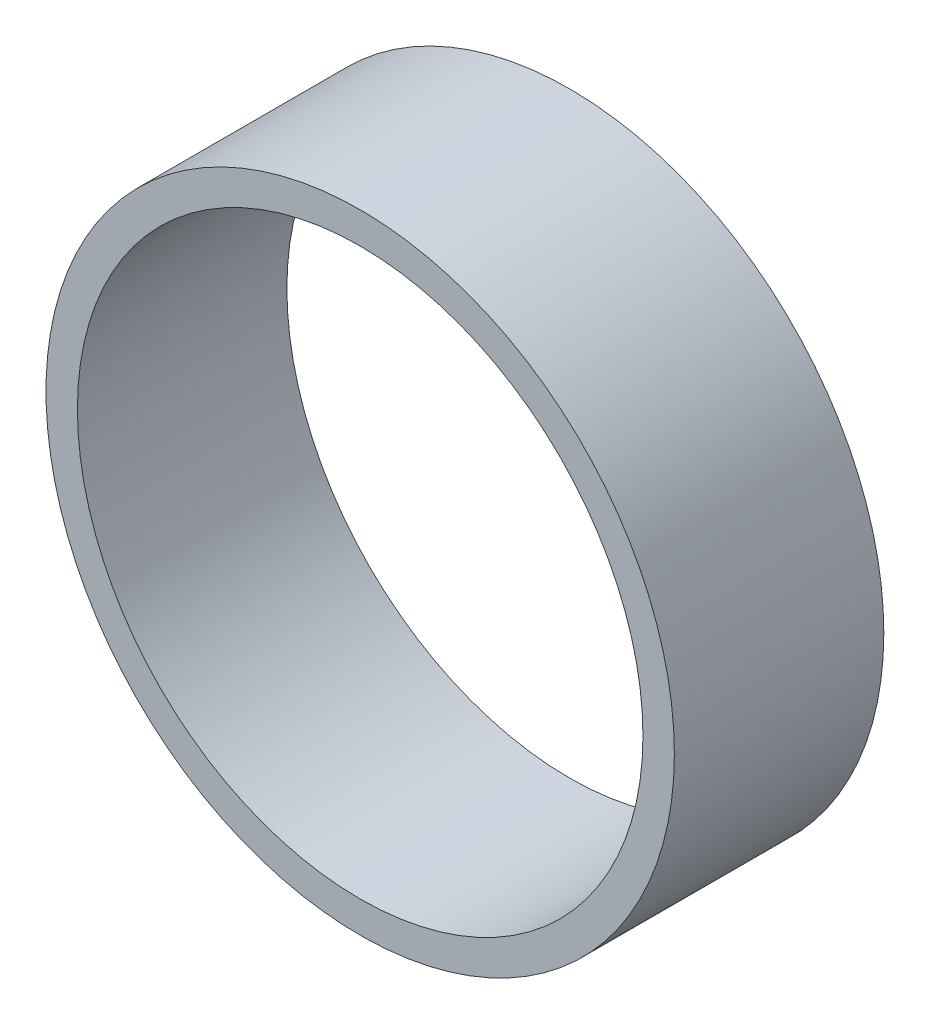
SolidWorks part; units mm, degrees
ref_plane "Płaszczyzna przednia" through (0, 0, 0) normal (0, 0, 1) x (1, 0, 0)
ref_plane "Płaszczyzna górna" through (0, 0, 0) normal (0, 1, 0) x (1, 0, 0)
ref_plane "Płaszczyzna prawa" through (0, 0, 0) normal (1, 0, 0) x (0, 0, -1)
sketch "Szkic2" plane through (0, 0, 0) normal (0, 0, 1) x (1, 0, 0)
  circle A0 centre (0, 0) radius 30
  circle A1 centre (0, 0) radius 27
  dimension "D1" = 60
  dimension "D2" = 54
extrude "Dodanie-wyciągnięcie1" add sketch "Szkic2" along normal blind 20
